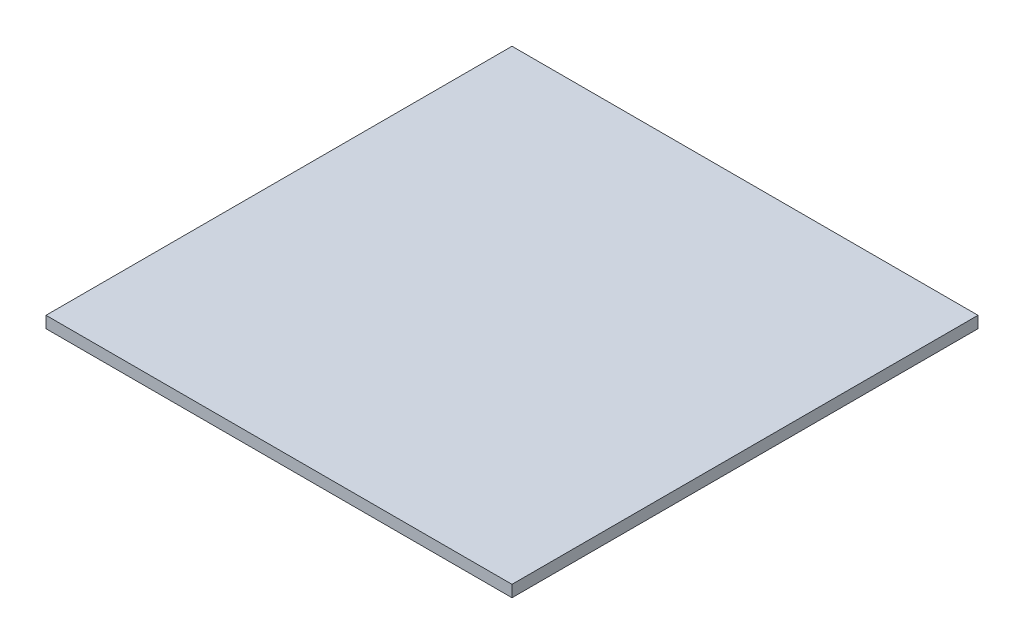
SolidWorks part; units mm, degrees
ref_plane "Plan de face" through (0, 0, 0) normal (0, 0, 1) x (1, 0, 0)
ref_plane "Plan de dessus" through (0, 0, 0) normal (0, 1, 0) x (1, 0, 0)
ref_plane "Plan de droite" through (0, 0, 0) normal (1, 0, 0) x (0, 0, -1)
sketch "Esquisse1" plane through (0, 0, 0) normal (0, 1, 0) x (1, 0, 0)
  line L1 (0, 0) -> (400, 0)
  line L2 (0, 0) -> (0, 400)
  line L3 (0, 400) -> (400, 400)
  line L4 (400, 0) -> (400, 400)
  dimension "D1" = 400
  dimension "D2" = 400
extrude "Extrusion1" add sketch "Esquisse1" along normal blind 10
